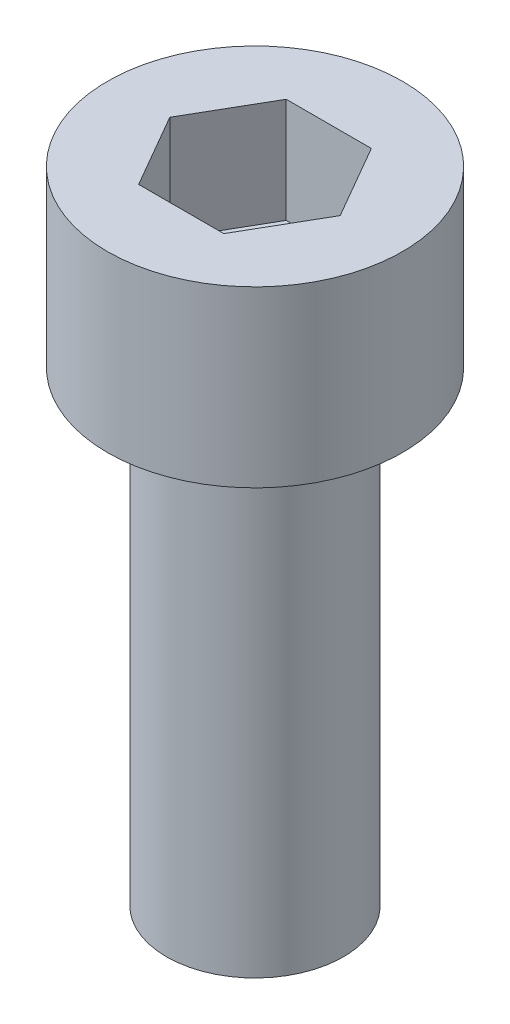
SolidWorks part; units mm, degrees
ref_plane "Front Plane" through (0, 0, 0) normal (0, 0, 1) x (1, 0, 0)
ref_plane "Top Plane" through (0, 0, 0) normal (0, 1, 0) x (1, 0, 0)
ref_plane "Right Plane" through (0, 0, 0) normal (1, 0, 0) x (0, 0, -1)
sketch "Sketch1" plane through (0, 0, 0) normal (0, 1, 0) x (1, 0, 0)
  circle A0 centre (0, 0) radius 1.5
  dimension "D1" = 3
extrude "Boss-Extrude1" add sketch "Sketch1" along normal blind 7.9
cosmetic thread "Cosmetic Thread1" parameters "D2"=2
sketch "Sketch3" plane through (0, 0, 0) normal (0, 0, 1) x (1, 0, 0)
  line L0 (0, 7.9) -> (2.5, 7.9)
  line L1 (1.5, 7.9) -> (-1.5, 7.9) construction
  line L2 (0, 10.85) -> (2.5, 10.85)
  line L3 (0, -2.75) -> (0, 2.75) construction
  line L4 (2.5, 10.85) -> (3.516, 10.85) construction
  line L5 (2.5, 7.9) -> (2.5, 10.85)
  line L6 (0, 7.9) -> (0, 10.85) construction
  line L7 (0, 7.9) -> (0, 10.85)
  line L8 (0, 10.85) -> (0, 17.3648) construction
  dimension "D1" = 5
  dimension "D2" = 2.95
revolve "Revolve1" add sketch "Sketch3" angle 360 about L7
sketch "Sketch4" plane through (0, 10.85, 0) normal (0, 1, 0) x (1, 0, 0)
  line L1 (1.4434, 0) -> (0.7217, 1.25)
  line L2 (0.7217, 1.25) -> (-0.7217, 1.25)
  line L3 (-0.7217, 1.25) -> (-1.4434, 0)
  line L4 (-1.4434, 0) -> (-0.7217, -1.25)
  line L5 (-0.7217, -1.25) -> (0.7217, -1.25)
  line L6 (0.7217, -1.25) -> (1.4434, 0)
  circle A0 centre (0, 0) radius 1.25 construction
  dimension "D1" = 2.5
extrude "Cut-Extrude1" cut sketch "Sketch4" against normal blind 1.778
